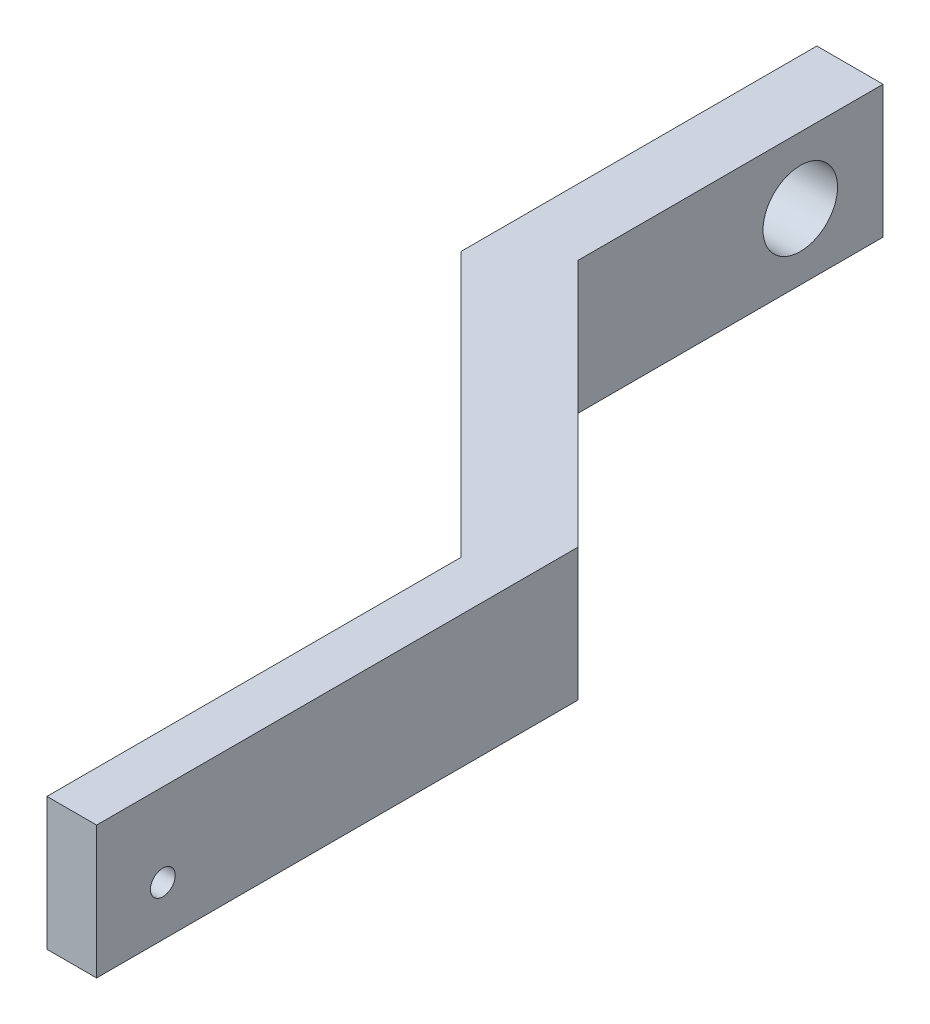
SolidWorks part; units mm, degrees
ref_plane "Front Plane" through (0, 0, 0) normal (0, 0, 1) x (1, 0, 0)
ref_plane "Top Plane" through (0, 0, 0) normal (0, 1, 0) x (1, 0, 0)
ref_plane "Right Plane" through (0, 0, 0) normal (1, 0, 0) x (0, 0, -1)
sketch "Sketch1" plane through (0, 0, 0) normal (0, 1, 0) x (1, 0, 0)
  line L0 (0, 0) -> (-3, 0)
  line L1 (-3, 0) -> (-3, 25)
  line L2 (-3, 25) -> (-19, 41)
  line L3 (-19, 41) -> (-19, 62.5)
  line L4 (-19, 62.5) -> (-15, 62.5)
  line L5 (-15, 62.5) -> (-15, 44.0711)
  line L6 (-15, 44.0711) -> (0, 29.0711)
  line L7 (0, 29.0711) -> (0, 0)
  dimension "D1" = 3
  dimension "D2" = 4
  dimension "D3" = 12
  dimension "D4" = 62.5
  dimension "D5" = 45
  dimension "D6" = 5
  dimension "D7" = 25
extrude "Boss-Extrude1" add sketch "Sketch1" along normal blind 8
sketch "Sketch2" plane through (-15, 0, 0) normal (1, 0, 0) x (0, 0, -1)
  line L0 (57.5, 4) -> (62.5, 4) construction
  line L2 (44.0711, 0) -> (62.5, 0) construction
  line L3 (62.5, 8) -> (62.5, 0) construction
  line L4 (44.0711, 8) -> (62.5, 8) construction
  line L5 (0, 8) -> (0, 0) construction
  line L6 (0, 0) -> (29.0711, 0) construction
  circle A0 centre (57.5, 4) radius 2.25
  circle A1 centre (4, 3) radius 0.75
  dimension "D1" = 1.5
  dimension "D2" = 4.5
  dimension "D5" = 4
  dimension "D6" = 3
  dimension "D3" = 4
  dimension "D4" = 5
extrude "Cut-Extrude1" cut sketch "Sketch2" against normal through all and the other way through all
